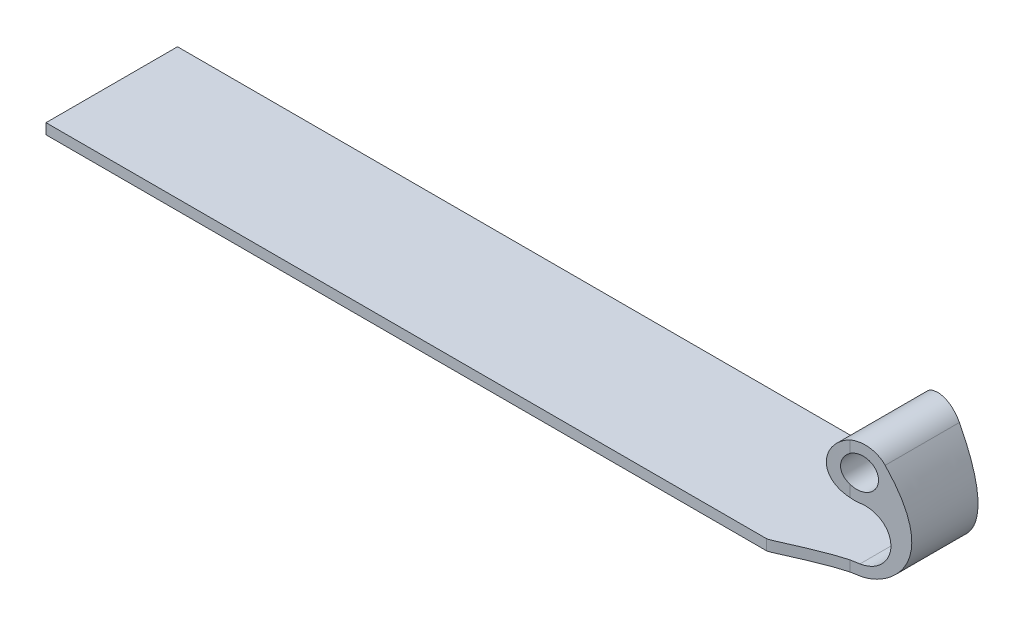
SolidWorks part; units mm, degrees
ref_plane "Front Plane" through (0, 0, 0) normal (0, 0, 1) x (1, 0, 0)
ref_plane "Top Plane" through (0, 0, 0) normal (0, 1, 0) x (1, 0, 0)
ref_plane "Right Plane" through (0, 0, 0) normal (1, 0, 0) x (0, 0, -1)
sketch "Sketch1" plane through (0, 0, 0) normal (0, 1, 0) x (1, 0, 0)
  line L1 (-38.1, -6.35) -> (38.1, -6.35)
  line L2 (-38.1, -6.35) -> (-38.1, 6.35)
  line L3 (-38.1, 6.35) -> (38.1, 6.35)
  line L4 (38.1, -6.35) -> (38.1, 6.35)
  line L5 (-38.1, -6.35) -> (38.1, 6.35) construction
  line L6 (-38.1, 6.35) -> (38.1, -6.35) construction
  point P0 (0, 0)
  dimension "D1" = 12.7
  dimension "D2" = 76.2
extrude "Boss-Extrude1" add sketch "Sketch1" along normal blind 1.016
sketch "Sketch2" plane through (0, 0, -6.35) normal (0, 0, -1) x (-1, 0, 0)
  line L1 (-38.1, 0) -> (38.1, 0) construction
  line L2 (-38.1, 0) -> (-40.0156, 0) construction
  line L3 (-40.0156, 0) -> (-42.8226, 1.8153) construction
  line L4 (-42.8226, 1.8153) -> (-43.8111, 4.9975) construction
  line L5 (-43.8111, 4.9975) -> (-40.1686, 10.1099) construction
  line L7 (-38.1, 1.016) -> (38.1, 1.016) construction
  line L8 (38.1, 1.016) -> (38.1, 0)
  line L9 (-38.1, 0) -> (38.1, 0)
  line L11 (38.1, 1.016) -> (38.1, 0) construction
  line L13 (-38.1, 1.016) -> (38.1, 1.016)
  arc A1 (-38.1, 6.096) -> (-40.1686, 10.1099) centre (-38.1, 8.636) ccw
  circle A2 centre (-38.1, 8.636) radius 1.524
  arc A6 (-38.1, 1.016) -> (-38.1, 6.096) centre (-38.1, 3.556) cw
  spline S0 degree 4 poles (-38.1, 0) (-40.0156, 0) (-42.8226, 1.8153) (-43.8111, 4.9975) (-40.1686, 10.1099) knots 0 0 0 0 0 1 1 1 1 1
  point P1 (0, 0)
  point P8 (-38.1, 1.016)
  dimension "D1" = 2.54
  dimension "D2" = 5.08
  dimension "D3" = 1.016
extrude "Boss-Extrude2" add sketch "Sketch2" against normal through all
sketch "Sketch3" plane through (0, 1.016, 0) normal (0, -1, 0) x (1, 0, 0)
  line L0 (24.4723, 6.35) -> (42.3541, 3.197)
  line L1 (-38.1, 6.35) -> (38.1, 6.35) construction
  line L2 (42.3541, 0) -> (38.1, 0) construction
  line L3 (42.3541, -6.35) -> (42.3541, 6.35) construction
  line L4 (38.1, 6.35) -> (38.1, -6.35) construction
  line L5 (24.4723, -6.35) -> (42.3541, -3.197)
  line L6 (24.4723, 6.35) -> (42.3541, 6.35)
  line L7 (42.3541, 6.35) -> (38.1, 6.35) construction
  line L8 (42.3541, 6.35) -> (42.3541, 3.197)
  line L9 (42.3541, -3.197) -> (42.3541, -6.35)
  line L10 (38.1, -6.35) -> (42.3541, -6.35) construction
  line L11 (42.3541, -6.35) -> (24.4723, -6.35)
  line L12 (39.2057, -3.7521) -> (36.3577, -3.8761) construction
  line L13 (36.3577, -3.8761) -> (31.9938, -6.35) construction
  line L14 (31.9938, -6.35) -> (31.4619, -6.35) construction
  line L15 (39.2057, 3.7521) -> (36.3577, 3.8761) construction
  line L16 (36.3577, 3.8761) -> (31.9938, 6.35) construction
  line L17 (31.9938, 6.35) -> (31.4619, 6.35) construction
  circle A0 centre (38.5441, 0) radius 3.81
  spline S0 degree 3 poles (39.2057, -3.7521) (36.3577, -3.8761) (31.9938, -6.35) (31.4619, -6.35) knots 0 0 0 0 1 1 1 1
  spline S1 degree 3 poles (39.2057, 3.7521) (36.3577, 3.8761) (31.9938, 6.35) (31.4619, 6.35) knots 0 0 0 0 1 1 1 1
  point P28 (39.7765, -3.8688)
  point P29 (39.7765, -3.8688)
  point P30 (0, 0)
  point P31 (41.1578, -3.5508)
  point P32 (0, 0)
  point P33 (40.4381, -3.7521)
  point P34 (39.0553, -3.996)
  point P35 (35.1066, 3.2651)
  point P36 (33.6706, 3.682)
  point P37 (27.4634, 6.35)
  point P38 (31.6597, -3.8848)
  point P39 (31.9938, -6.35)
  point P40 (34.0419, -3.4333)
  point P41 (31.4619, 6.35)
  point P42 (36.1451, 4.2918)
  point P43 (37.742, 4.0102)
  point P44 (0, 0)
  point P45 (35.0264, 3.649)
  point P46 (38.1, 3.784)
  point P47 (37.0698, 4.1287)
  point P48 (0, 0)
  point P49 (0, 0)
  point P50 (34.5489, 3.8169)
  point P51 (36.3577, 3.8761)
  line M26 (38.1, 6.35) -> (38.1, -6.35)
  line M27 (38.1, -6.35) -> (-38.1, -6.35)
  dimension "D2" = 7.62
  dimension "D1" = 10
extrude "Cut-Extrude1" cut sketch "Sketch3" against normal through all and the other way blind 10 contours S0 L5 M26 M27 | L9 L11 L5 M26 | L6 L8 L0 M26 | L0 S1 L6 M26
